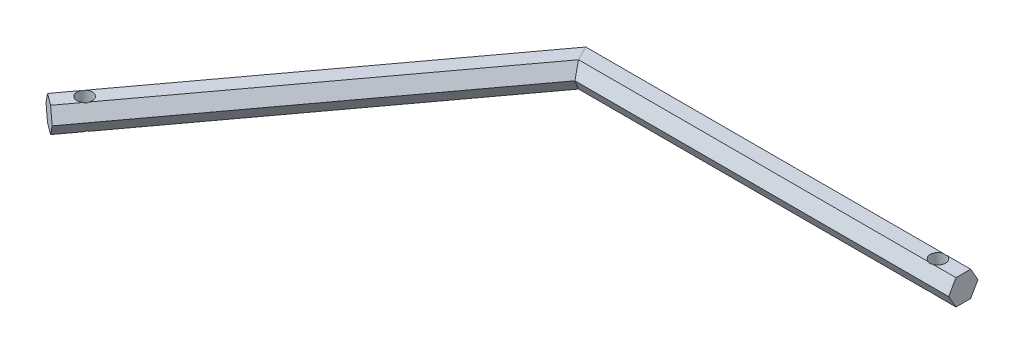
SolidWorks part; units mm, degrees
ref_plane "Front Plane" through (0, 0, 0) normal (0, 0, 1) x (1, 0, 0)
ref_plane "Top Plane" through (0, 0, 0) normal (0, 1, 0) x (1, 0, 0)
ref_plane "Right Plane" through (0, 0, 0) normal (1, 0, 0) x (0, 0, -1)
sketch "Sketch1" plane through (0, 0, 0) normal (0, 1, 0) x (1, 0, 0)
  line L0 (0, 0) -> (150, 0)
  line L1 (0, 0) -> (-89.2234, -120.5785)
  dimension "D1" = 53.5
  dimension "D2" = 150
ref_plane "Plane1" through (-89.2234, 0, 120.5785) normal (-0.5948, 0, 0.8039) x (0.8039, 0, 0.5948)
sketch "Sketch2" plane through (-89.2234, 0, 120.5785) normal (-0.5948, 0, 0.8039) x (0.8039, 0, 0.5948)
  line L0 (0, 0) -> (120.5785, 0) construction
  line L1 (2.8868, -5) -> (5.7735, 0)
  line L2 (5.7735, 0) -> (2.8868, 5)
  line L3 (2.8868, 5) -> (-2.8868, 5)
  line L4 (-2.8868, 5) -> (-5.7735, 0)
  line L5 (-5.7735, 0) -> (-2.8868, -5)
  line L6 (-2.8868, -5) -> (2.8868, -5)
  circle A0 centre (0, 0) radius 5 construction
  point P1 (3.1626, 4.8302)
  point P10 (0, 0)
  dimension "D1" = 10
sweep "Sweep2" add profiles "Sketch2" path "Sketch1"
sketch "Sketch4" plane through (0, 5, 0) normal (0, 1, 0) x (1, 0, 0)
  line L0 (150, -2.8868) -> (150, 2.8868) construction
  circle A0 centre (140, 0) radius 3
  point P2 (0, 0)
  point P5 (0, 0)
  point P6 (0, 0)
  point P7 (150, 0)
  dimension "D1" = 6
  dimension "D2" = 10
extrude "Cut-Extrude1" cut sketch "Sketch4" against normal through all
ref_plane "Plane2" through (0, 0, 0) normal (0.893, 0, -0.4501) x (-0.4501, 0, -0.893)
mirror "Mirror1" about plane through (0, 0, 0) normal (0.893, 0, -0.4501) of "Cut-Extrude1"
